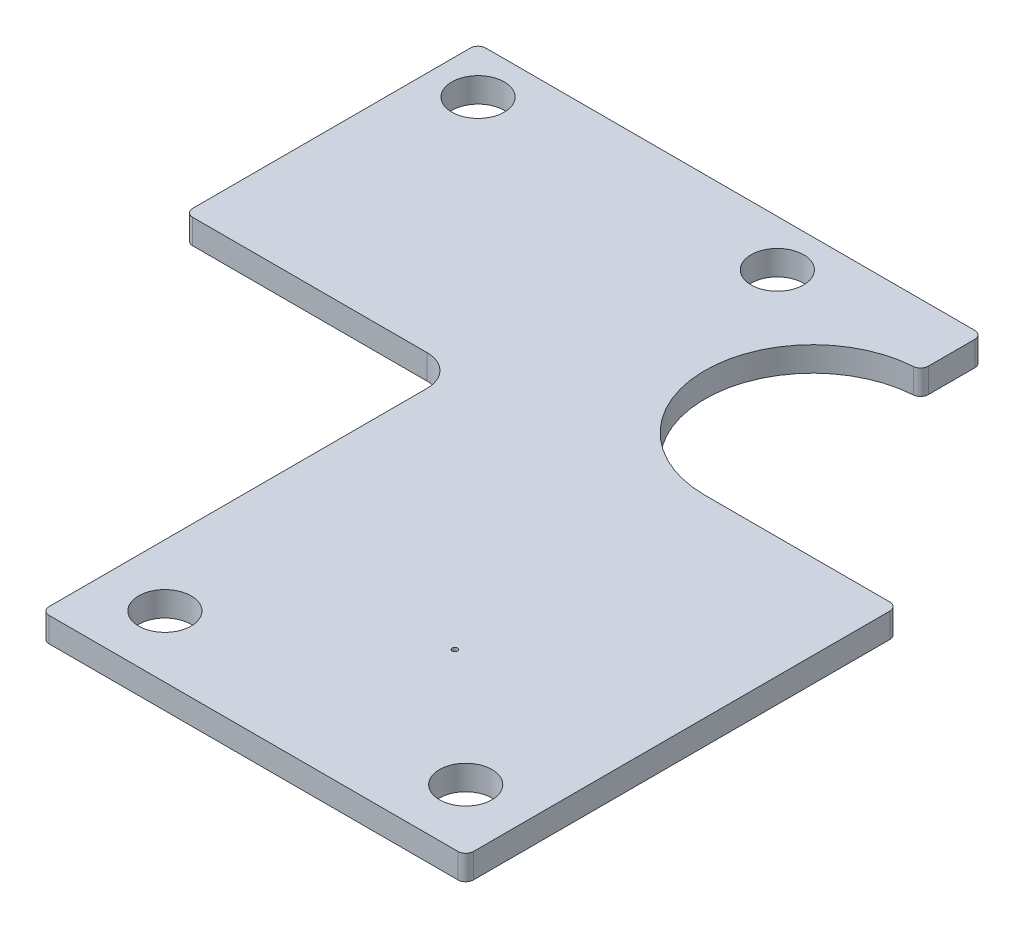
SolidWorks part; units mm, degrees
ref_plane "Front Plane" through (0, 0, 0) normal (0, 0, 1) x (1, 0, 0)
ref_plane "Top Plane" through (0, 0, 0) normal (0, 1, 0) x (1, 0, 0)
ref_plane "Right Plane" through (0, 0, 0) normal (1, 0, 0) x (0, 0, -1)
sketch "Sketch1" plane through (0, 0, 0) normal (0, 1, 0) x (1, 0, 0)
  line L4 (0.0326, 32.5901) -> (0.0326, 51.5901)
  line L5 (0.0326, 51.5901) -> (32.7326, 51.5901)
  line L6 (32.7326, 47.5901) -> (32.7326, 51.5901)
  line L7 (32.7326, 33.5901) -> (45.2326, 33.5901)
  line L8 (45.2326, 33.5901) -> (45.2326, 5.5901)
  line L9 (45.2326, 5.5901) -> (17.7326, 5.5901)
  line L10 (17.7326, 5.5901) -> (17.7326, 32.5901)
  line L11 (17.7326, 32.5901) -> (0.0326, 32.5901)
  arc A0 (32.7326, 47.5901) -> (32.7326, 33.5901) centre (32.7326, 40.5901) ccw
  dimension "D1" = 14
  dimension "D2" = 45.2326
  dimension "D3" = 51.5901
  dimension "D4" = 27.5
  dimension "D5" = 19
extrude "Boss-Extrude1" add sketch "Sketch1" along normal blind 1.6
fillet "Fillet1" radius 0.5 7 edges at (32.7326, 0.8, -47.5901) (0.0326, 0.8, -51.5901) (0.0326, 0.8, -32.5901) (32.7326, 0.8, -51.5901) (45.2326, 0.8, -33.5901) (17.7326, 0.8, -5.5901) (45.2326, 0.8, -5.5901)
fillet "Fillet2" radius 2 1 edges at (17.7326, 0.8, -32.5901)
hole_wizard "M3 Clearance Hole1" positions "Sketch2" profile "Sketch3" hole size "M3" standard "ANSI Metric" end condition through all
sketch "Sketch2" plane through (0, 1.6, 0) normal (0, 1, 0) x (1, 0, 0)
  line L0 (45.2326, 6.0901) -> (45.2326, 33.0901) construction
  line L1 (17.7326, 30.5901) -> (17.7326, 6.0901) construction
  point P0 (3.0326, 48.5901)
  point P3 (22.4326, 48.5901)
  point P6 (21.7326, 9.5901)
  point P9 (41.2326, 9.5901)
  dimension "D1" = 4
  dimension "D2" = 4
sketch "Sketch3" plane through (3.0326, 1.6, -48.5901) normal (1, 0, 0) x (0, 0, 1)
  line L0 (0, 0) -> (0, 1.6)
  line L1 (0, 1.6) -> (1.7, 1.6)
  line L2 (1.7, 1.6) -> (1.7, 0)
  line L5 (1.7, 0) -> (0, 0)
  line L11 (0, -6.35) -> (0, 107.95) construction
  dimension "Thru Hole Dia." = 3.4
  dimension "Thru Hole Depth" = 1.6
sketch "Sketch4" plane through (0, 1.6, 0) normal (0, 1, 0) x (1, 0, 0)
  circle A0 centre (33.2976, 16.8251) radius 0.175
extrude "Cut-Extrude1" cut sketch "Sketch4" against normal through all
